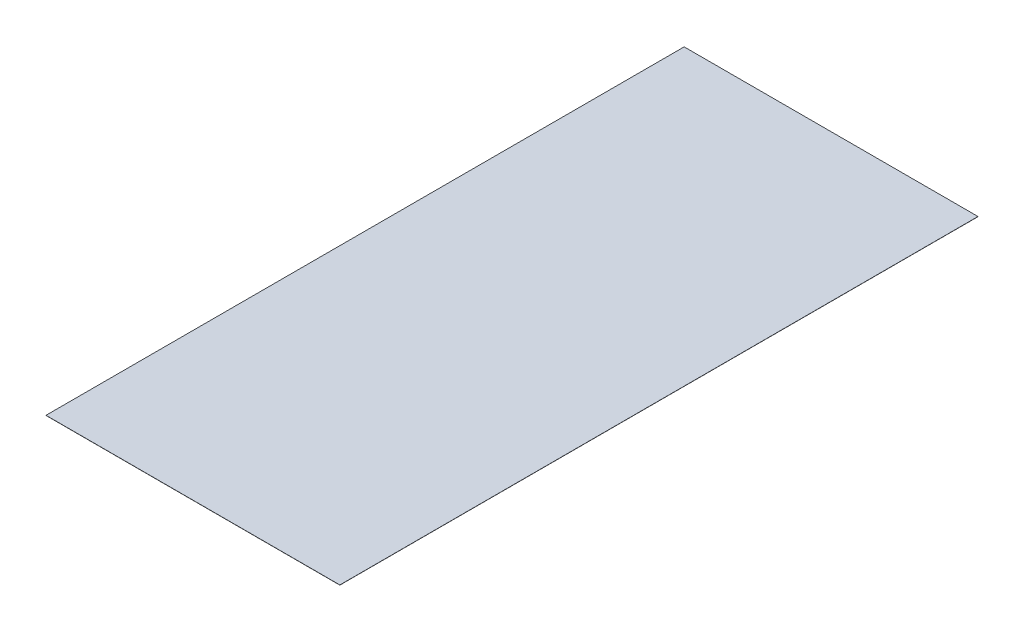
SolidWorks part; units mm, degrees
material "Galvanized Steel"
ref_plane "Front Plane" through (0, 0, 0) normal (0, 0, 1) x (1, 0, 0)
ref_plane "Top Plane" through (0, 0, 0) normal (0, 1, 0) x (1, 0, 0)
ref_plane "Right Plane" through (0, 0, 0) normal (1, 0, 0) x (0, 0, -1)
sketch "Sketch1" plane through (0, 0, 0) normal (0, 0, 1) x (1, 0, 0)
  line L0 (54.3422, 542.2813) -> (568.0918, 609.9177) construction
  line L1 (-19.5283, 1100.9866) -> (54.0391, 542.1866)
  line L2 (568.0918, 609.9177) -> (429.9738, 110.4813) construction
  line L3 (-19.2252, 1101.0813) -> (54.3422, 542.2813)
  line L4 (429.6707, 110.3866) -> (429.9738, 110.4813)
  line L5 (-19.5283, 1100.9866) -> (-19.2252, 1101.0813)
  arc A0 (54.0391, 542.1866) -> (429.6707, 110.3866) centre (567.7887, 609.823) ccw
  arc A1 (54.3422, 542.2813) -> (429.9738, 110.4813) centre (568.0918, 609.9177) ccw
  point P4 (429.6707, 110.3866)
  dimension "D3" = 0.3175
extrude "Boss-Extrude1" [suppressed] add sketch "Sketch1" along normal blind 536.448
sketch "Sketch2" plane through (0, 0, 0) normal (0, 1, 0) x (1, 0, 0)
  line L1 (0, 0) -> (536.448, 0)
  line L2 (0, 0) -> (0, 1165.0769)
  line L3 (0, 1165.0769) -> (536.448, 1165.0769)
  line L4 (536.448, 0) -> (536.448, 1165.0769)
  dimension "D1" = 1165.0769
  dimension "D2" = 536.448
extrude "Boss-Extrude2" add sketch "Sketch2" along normal blind 0.3175
